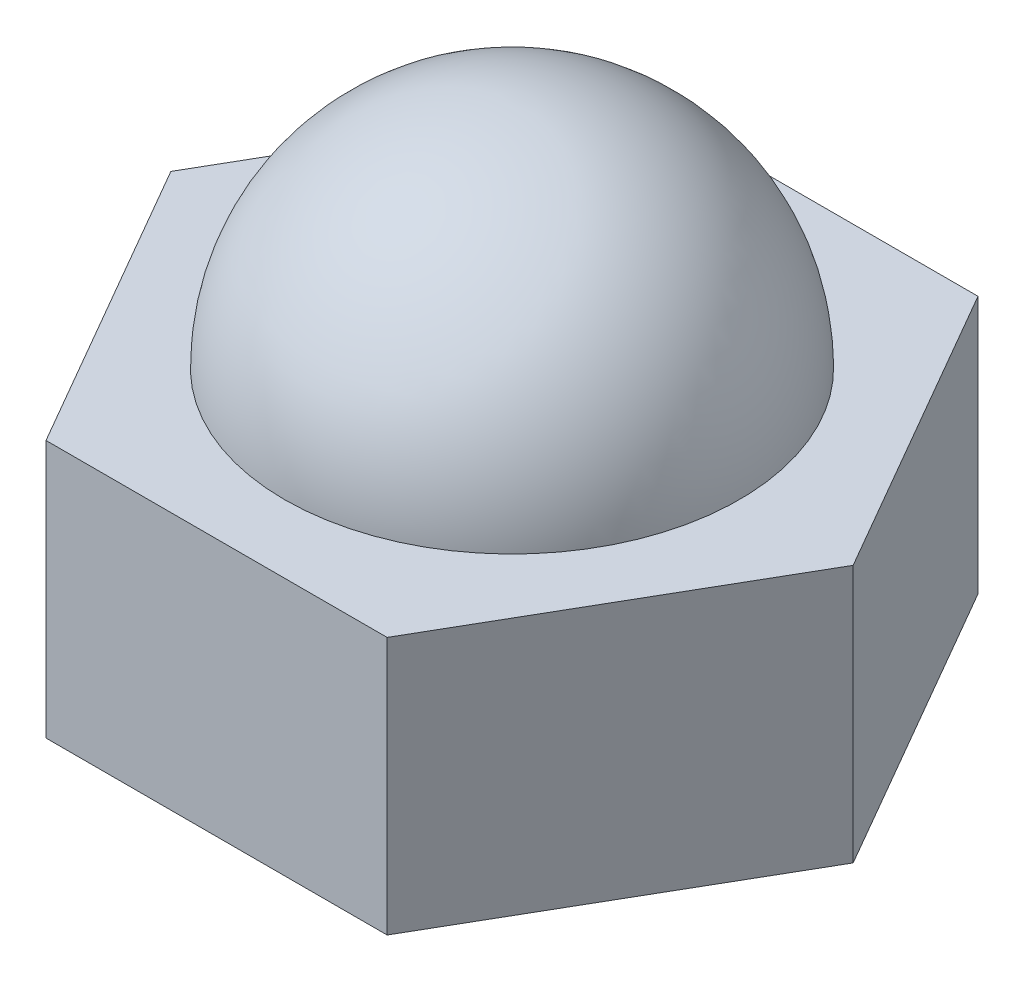
SolidWorks part; units mm, degrees
material "Cast Stainless Steel"
ref_plane "Front Plane" through (0, 0, 0) normal (0, 0, 1) x (1, 0, 0)
ref_plane "Top Plane" through (0, 0, 0) normal (0, 1, 0) x (1, 0, 0)
ref_plane "Right Plane" through (0, 0, 0) normal (1, 0, 0) x (0, 0, -1)
sketch "Sketch1" plane through (0, 0, 0) normal (0, 1, 0) x (1, 0, 0)
  line L1 (2.25, 3.8971) -> (-2.25, 3.8971)
  line L2 (-2.25, 3.8971) -> (-4.5, 0)
  line L3 (-4.5, 0) -> (-2.25, -3.8971)
  line L4 (-2.25, -3.8971) -> (2.25, -3.8971)
  line L5 (2.25, -3.8971) -> (4.5, 0)
  line L6 (4.5, 0) -> (2.25, 3.8971)
  circle A0 centre (0, 0) radius 3.8971 construction
  circle A1 centre (0, 0) radius 3.8971 construction
  dimension "D2" = 7.7942
extrude "Boss-Extrude1" add sketch "Sketch1" along normal blind 3.4
sketch "Sketch2" plane through (0, 3.4, 0) normal (0, 1, 0) x (1, 0, 0)
  line L0 (0, 3) -> (0, -3)
  arc A0 (0, -3) -> (0, 3) centre (0, 0) ccw
  dimension "D1" = 6
revolve "Revolve1" add sketch "Sketch2" angle 360 about L0
sketch "Sketch4" plane through (0, 0, 0) normal (0, -1, 0) x (1, 0, 0)
  circle A0 centre (0, 0) radius 2.5
  dimension "D1" = 5
extrude "Cut-Extrude1" cut sketch "Sketch4" against normal blind 1.2
